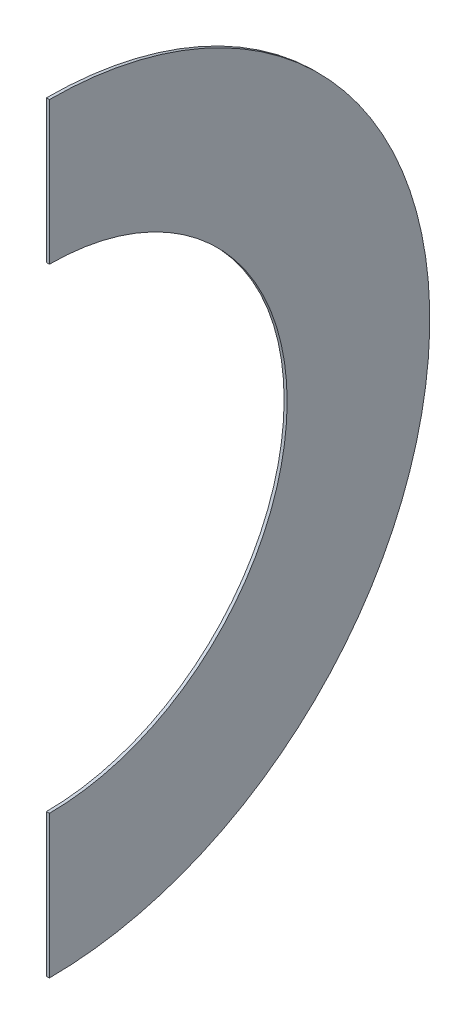
SolidWorks part; units mm, degrees
ref_plane "Front Plane" through (0, 0, 0) normal (0, 0, 1) x (1, 0, 0)
ref_plane "Top Plane" through (0, 0, 0) normal (0, 1, 0) x (1, 0, 0)
ref_plane "Right Plane" through (0, 0, 0) normal (1, 0, 0) x (0, 0, -1)
sketch "Sketch1" plane through (0, 0, 0) normal (1, 0, 0) x (0, 0, -1)
  line L0 (0, 200) -> (0, -200)
  circle A0 centre (0, 0) radius 200
  circle A1 centre (0, 0) radius 125
extrude "Boss-Extrude1" add sketch "Sketch1" along normal blind 1.5875 contours A1 L0 A0
